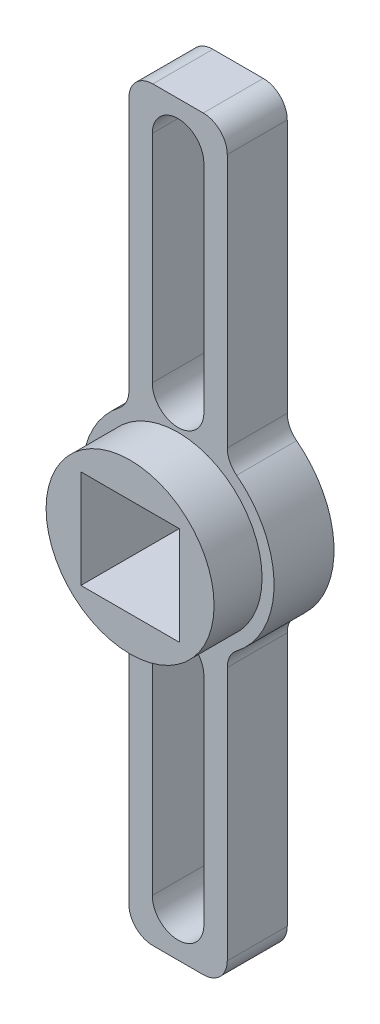
SolidWorks part; units mm, degrees
ref_plane "前视基准面" through (0, 0, 0) normal (0, 0, 1) x (1, 0, 0)
ref_plane "上视基准面" through (0, 0, 0) normal (0, 1, 0) x (1, 0, 0)
ref_plane "右视基准面" through (0, 0, 0) normal (1, 0, 0) x (0, 0, -1)
sketch "草图1" plane through (0, 0, 0) normal (0, 0, 1) x (1, 0, 0)
  line L1 (4.1, -4.1) -> (-4.1, -4.1)
  line L2 (4.1, -4.1) -> (4.1, 4.1)
  line L3 (4.1, 4.1) -> (-4.1, 4.1)
  line L4 (-4.1, -4.1) -> (-4.1, 4.1)
  line L5 (4.1, -4.1) -> (-4.1, 4.1) construction
  line L6 (4.1, 4.1) -> (-4.1, -4.1) construction
  circle A0 centre (0, 0) radius 8
  point P0 (0, 0)
  dimension "D3" = 16
  dimension "D1" = 8.2
  dimension "D2" = 8.2
extrude "凸台-拉伸1" add sketch "草图1" along normal blind 5
sketch "草图2" plane through (0, 4.1, 0) normal (0, -1, 0) x (1, 0, 0)
  line L4 (-4.1, 0) -> (4.1, 0)
  line L5 (4.1, 0) -> (4.1, 5)
  line L6 (4.1, 5) -> (-4.1, 5)
  line L7 (-4.1, 5) -> (-4.1, 0)
  line L8 (-4.1, 0) -> (4.1, 0)
  line L9 (4.1, 0) -> (4.1, 5)
  line L10 (4.1, 5) -> (-4.1, 5)
  line L11 (-4.1, 5) -> (-4.1, 0)
  dimension "D1" = 0
extrude "凸台-拉伸2" add sketch "草图2" against normal blind 27
sketch "草图3" plane through (0, -4.1, 0) normal (0, 1, 0) x (1, 0, 0)
  line L4 (4.1, 0) -> (-4.1, 0)
  line L5 (-4.1, 0) -> (-4.1, -5)
  line L6 (-4.1, -5) -> (4.1, -5)
  line L7 (4.1, -5) -> (4.1, 0)
  line L8 (4.1, 0) -> (-4.1, 0)
  line L9 (-4.1, 0) -> (-4.1, -5)
  line L10 (-4.1, -5) -> (4.1, -5)
  line L11 (4.1, -5) -> (4.1, 0)
  dimension "D1" = 0
extrude "凸台-拉伸3" add sketch "草图3" against normal blind 27
sketch "草图4" plane through (0, 0, 5) normal (0, 0, 1) x (1, 0, 0)
  line L0 (4.1, 4.1) -> (-4.1, 4.1) construction
  line L1 (4.1, -4.1) -> (4.1, 4.1) construction
  line L2 (-4.1, -4.1) -> (4.1, -4.1) construction
  line L3 (-4.1, 4.1) -> (-4.1, -4.1) construction
  line L4 (4.1, 4.1) -> (-4.1, 4.1)
  line L5 (4.1, -4.1) -> (4.1, 4.1)
  line L6 (-4.1, -4.1) -> (4.1, -4.1)
  line L7 (-4.1, 4.1) -> (-4.1, -4.1)
  circle A0 centre (0, 0) radius 7
  dimension "D1" = 14
extrude "凸台-拉伸4" add sketch "草图4" along normal blind 4
sketch "草图5" plane through (0, 0, 5) normal (0, 0, 1) x (1, 0, 0)
  line L0 (0, 27.5) -> (0, 9.5) construction
  line L1 (2.15, 27.5) -> (2.15, 9.5)
  line L2 (-2.15, 27.5) -> (-2.15, 9.5)
  arc A0 (2.15, 27.5) -> (-2.15, 27.5) centre (0, 27.5) ccw
  arc A1 (-2.15, 9.5) -> (2.15, 9.5) centre (0, 9.5) ccw
  point P3 (0, 18.5)
  dimension "D3" = 2.15
  dimension "D1" = 18
  dimension "D2" = 18.5
extrude "切除-拉伸1" cut sketch "草图5" against normal through all
mirror "镜向1" about plane through (0, 0, 0) normal (0, 1, 0) of "切除-拉伸1"
fillet "圆角1" radius 2 4 edges at (4.1, -6.8695, 2.5) (-4.1, -6.8695, 2.5) (-4.1, 6.8695, 2.5) (4.1, 6.8695, 2.5)
fillet "圆角2" radius 2 4 edges at (4.1, -31.1, 2.5) (-4.1, -31.1, 2.5) (4.1, 31.1, 2.5) (-4.1, 31.1, 2.5)
